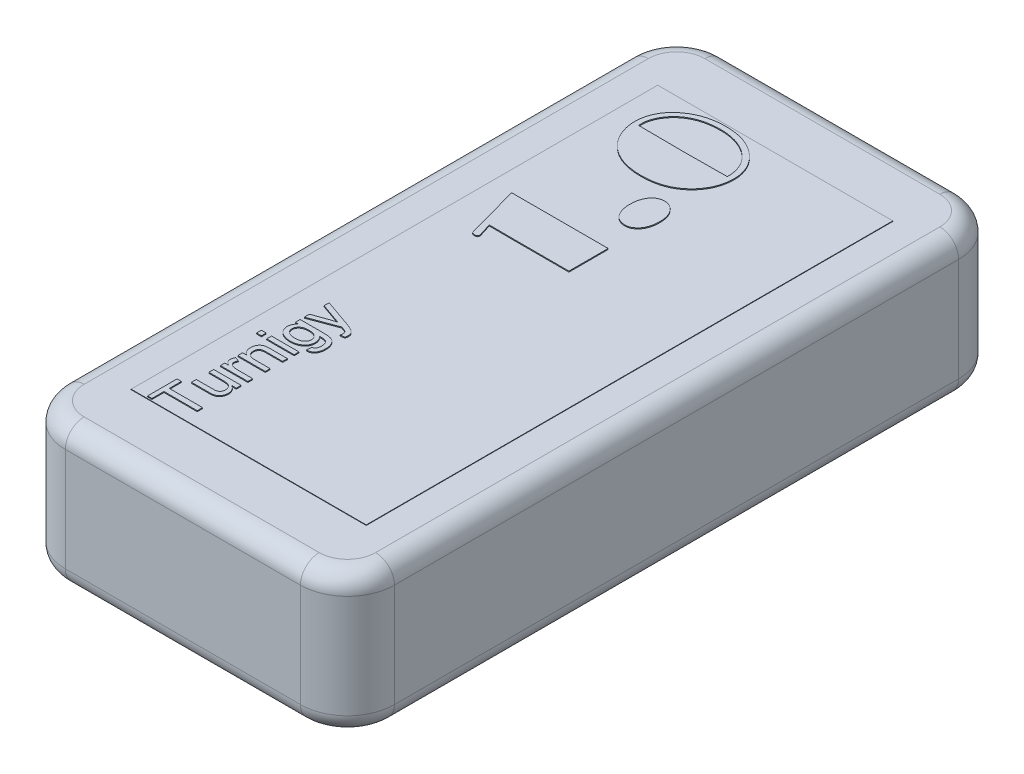
SolidWorks part; units mm, degrees
material "ABS"
ref_plane "Спереди" through (0, 0, 0) normal (0, 0, 1) x (1, 0, 0)
ref_plane "Сверху" through (0, 0, 0) normal (0, 1, 0) x (1, 0, 0)
ref_plane "Справа" through (0, 0, 0) normal (1, 0, 0) x (0, 0, -1)
sketch "Эскиз1" plane through (0, 0, 0) normal (0, 1, 0) x (1, 0, 0)
  line L1 (-17.5, 35) -> (17.5, 35)
  line L2 (-17.5, 35) -> (-17.5, -35)
  line L3 (-17.5, -35) -> (17.5, -35)
  line L4 (17.5, 35) -> (17.5, -35)
  line L5 (-17.5, 35) -> (17.5, -35) construction
  line L6 (-17.5, -35) -> (17.5, 35) construction
  point P0 (0, 0)
  dimension "D1" = 70
  dimension "D2" = 35
extrude "Бобышка-Вытянуть1" add sketch "Эскиз1" along normal blind 15
fillet "Скругление1" radius 5 1 edges at (17.5, 7.5, 35)
fillet "Скругление2" radius 5 1 edges at (-17.5, 7.5, 35)
fillet "Скругление3" radius 5 1 edges at (17.5, 7.5, -35)
fillet "Скругление4" radius 5 1 edges at (-17.5, 7.5, -35)
fillet "Скругление5" radius 2 8 edges at (16.0355, 15, 33.5355) (0, 15, 35) (-16.0355, 15, 33.5355) (-17.5, 15, 0) (-16.0355, 15, -33.5355) (0, 15, -35) (16.0355, 15, -33.5355) (17.5, 15, 0)
fillet "Скругление6" radius 2 8 edges at (16.0355, 0, 33.5355) (0, 0, 35) (-16.0355, 0, 33.5355) (-17.5, 0, 0) (-16.0355, 0, -33.5355) (0, 0, -35) (16.0355, 0, -33.5355) (17.5, 0, 0)
sketch "Эскиз2" plane through (0, 15, 0) normal (0, 1, 0) x (1, 0, 0)
  line L0 (12.5, 33) -> (-12.5, 33) construction
  line L1 (-12.5, -28) -> (12.5, -28)
  line L2 (-12.5, -28) -> (-12.5, 28)
  line L3 (-12.5, 28) -> (12.5, 28)
  line L4 (12.5, -28) -> (12.5, 28)
  line L5 (-12.5, -28) -> (12.5, 28) construction
  line L6 (-12.5, 28) -> (12.5, -28) construction
  line L7 (15.5, -30) -> (15.5, 30) construction
  point P0 (0, 0)
  dimension "D1" = 5
  dimension "D2" = 3
extrude "Бобышка-Вытянуть2" add sketch "Эскиз2" along normal blind 0.05 separate body
sketch "Эскиз3" plane through (0, 15.05, 0) normal (0, 1, 0) x (1, 0, 0)
  line L0 (0, -28) -> (0, 28) construction
  line L1 (-12.5, -28) -> (12.5, -28) construction
  line L2 (12.5, 28) -> (-12.5, 28) construction
  line L3 (-6.9069, -28) -> (-6.9069, 28) construction
  text T0 "Turnigy"
  text T1 "1.0" font "Broadway" height 10
extrude "Бобышка-Вытянуть3" add sketch "Эскиз3" along normal blind 0.1
